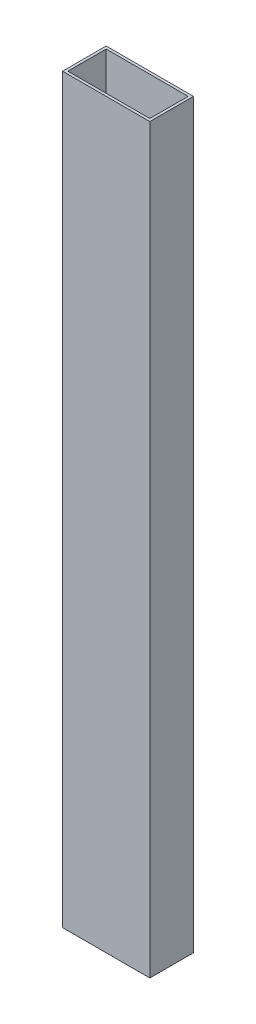
SolidWorks part; units mm, degrees
ref_plane "Front Plane" through (0, 0, 0) normal (0, 0, 1) x (1, 0, 0)
ref_plane "Top Plane" through (0, 0, 0) normal (0, 1, 0) x (1, 0, 0)
ref_plane "Right Plane" through (0, 0, 0) normal (1, 0, 0) x (0, 0, -1)
sketch "Sketch1" plane through (0, 0, 0) normal (0, 1, 0) x (1, 0, 0)
  line L1 (-21.4648, 13.0577) -> (29.3352, 13.0577)
  line L2 (-21.4648, 13.0577) -> (-21.4648, -12.3423)
  line L3 (-21.4648, -12.3423) -> (29.3352, -12.3423)
  line L4 (29.3352, 13.0577) -> (29.3352, -12.3423)
  line L5 (-19.9408, 11.5337) -> (27.8112, 11.5337)
  line L6 (-19.9408, 11.5337) -> (-19.9408, -10.8183)
  line L7 (-19.9408, -10.8183) -> (27.8112, -10.8183)
  line L8 (27.8112, 11.5337) -> (27.8112, -10.8183)
  dimension "D1" = 50.8
  dimension "D2" = 25.4
  dimension "D3" = 1.524
  dimension "D4" = 1.524
  dimension "D5" = 1.524
  dimension "D6" = 1.524
extrude "Boss-Extrude1" add sketch "Sketch1" along normal blind 432.054
